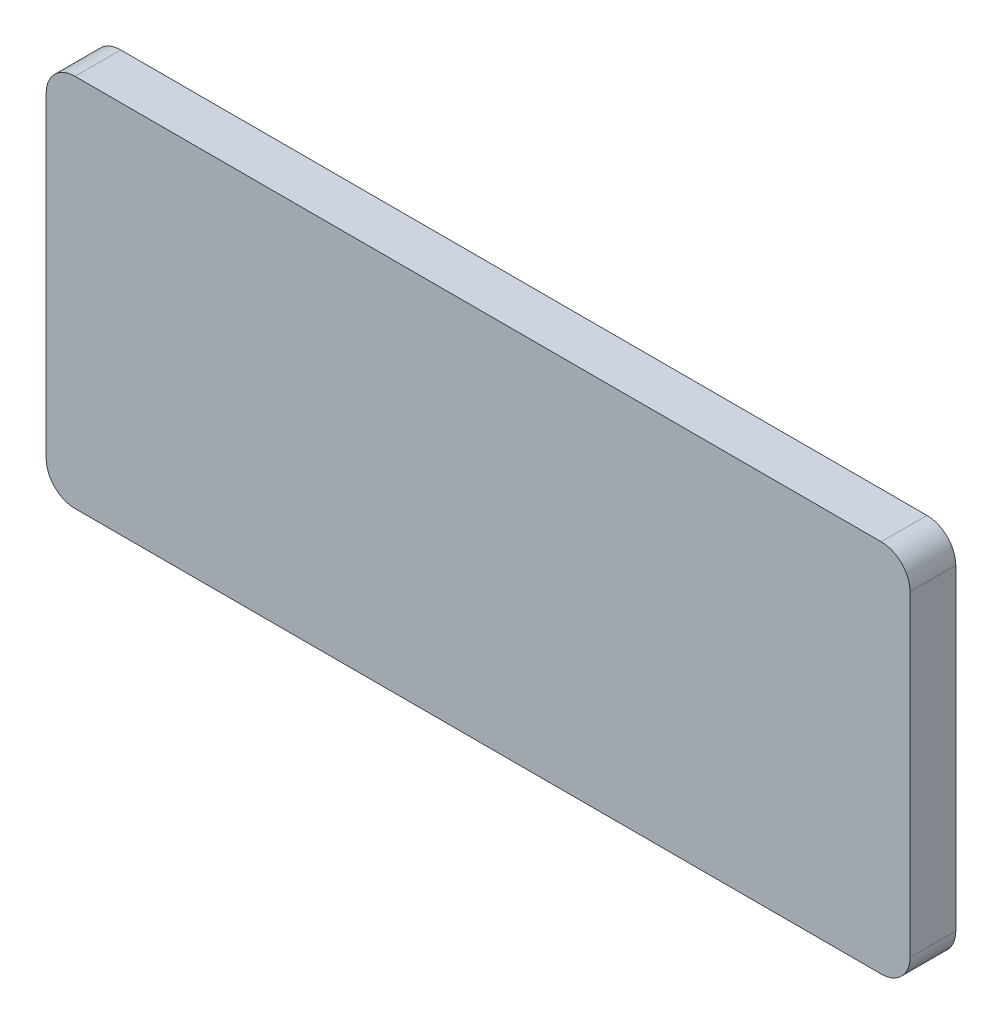
SolidWorks part; units mm, degrees
ref_plane "Front Plane" through (0, 0, 0) normal (0, 0, 1) x (1, 0, 0)
ref_plane "Top Plane" through (0, 0, 0) normal (0, 1, 0) x (1, 0, 0)
ref_plane "Right Plane" through (0, 0, 0) normal (1, 0, 0) x (0, 0, -1)
sketch "Sketch1" plane through (0, 0, 0) normal (0, 0, 1) x (1, 0, 0)
  line L1 (0, 0) -> (-60, 0)
  line L2 (0, 0) -> (0, 26)
  line L3 (0, 26) -> (-60, 26)
  line L4 (-60, 0) -> (-60, 26)
  dimension "D1" = 60
  dimension "D2" = 26
extrude "Boss-Extrude1" add sketch "Sketch1" along normal blind 3.175
fillet "Fillet1" radius 2 4 edges at (0, 26, 1.5875) (0, 0, 1.5875) (-60, 0, 1.5875) (-60, 26, 1.5875)
